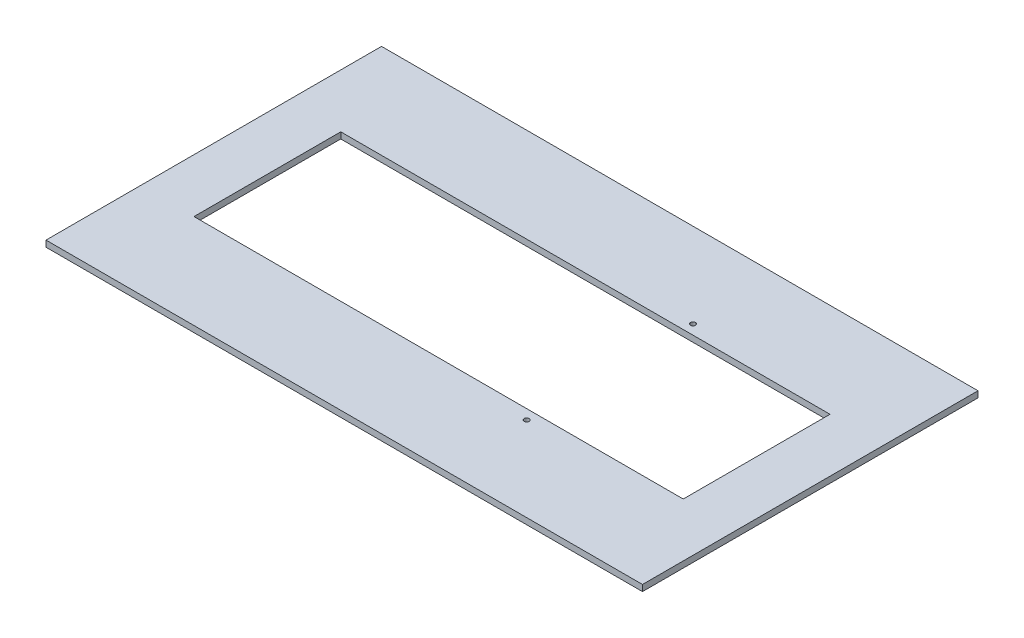
SolidWorks part; units mm, degrees
ref_plane "Front Plane" through (0, 0, 0) normal (0, 0, 1) x (1, 0, 0)
ref_plane "Top Plane" through (0, 0, 0) normal (0, 1, 0) x (1, 0, 0)
ref_plane "Right Plane" through (0, 0, 0) normal (1, 0, 0) x (0, 0, -1)
sketch "Sketch1" plane through (0, 0, 0) normal (0, 1, 0) x (1, 0, 0)
  line L1 (0, 0) -> (609.6, 0)
  line L2 (0, 0) -> (0, 342.9)
  line L3 (0, 342.9) -> (609.6, 342.9)
  line L4 (609.6, 0) -> (609.6, 342.9)
  line L5 (54.8, 246.45) -> (554.8, 246.45)
  line L6 (54.8, 246.45) -> (54.8, 96.45)
  line L7 (54.8, 96.45) -> (554.8, 96.45)
  line L8 (554.8, 246.45) -> (554.8, 96.45)
  circle A0 centre (404.8, 256.45) radius 2.555
  circle A1 centre (404.8, 86.45) radius 2.555
  point P4 (304.8, 246.45)
  point P10 (304.8, 342.9)
  point P11 (554.8, 171.45)
  point P12 (609.6, 171.45)
  dimension "D5" = 5.11
  dimension "D6" = 150
  dimension "D1" = 342.9
  dimension "D2" = 609.6
  dimension "D3" = 500
  dimension "D4" = 150
  dimension "D7" = 170
  dimension "D8" = 10
extrude "Boss-Extrude1" add sketch "Sketch1" along normal blind 6.35
sketch "Sketch2" plane through (0, 6.35, 0) normal (0, 1, 0) x (1, 0, 0)
  line L0 (511.8, 342.9) -> (511.8, 246.45)
  line L1 (554.8, 246.45) -> (54.8, 246.45) construction
  line L2 (609.6, 342.9) -> (0, 342.9) construction
  line L3 (554.8, 96.45) -> (554.8, 246.45) construction
  line L4 (511.8, 0) -> (511.8, 96.45)
  line L5 (54.8, 96.45) -> (554.8, 96.45) construction
  line L6 (0, 0) -> (609.6, 0) construction
  line L7 (411.8, 0) -> (411.8, 96.45)
  line L8 (411.8, 342.9) -> (411.8, 246.45)
  line L9 (311.8, 0) -> (311.8, 96.45)
  line L10 (311.8, 342.9) -> (311.8, 246.45)
  line L11 (211.8, 0) -> (211.8, 96.45)
  line L12 (211.8, 342.9) -> (211.8, 246.45)
  line L13 (111.8, 0) -> (111.8, 96.45)
  line L14 (111.8, 342.9) -> (111.8, 246.45)
  line L15 (461.8, 96.45) -> (461.8, 46.45)
  line L16 (361.8, 96.45) -> (361.8, 46.45)
  line L17 (261.8, 96.45) -> (261.8, 46.45)
  line L18 (161.8, 96.45) -> (161.8, 46.45)
  line L19 (361.8, 296.45) -> (361.8, 246.45)
  line L20 (261.8, 296.45) -> (261.8, 246.45)
  line L21 (161.8, 296.45) -> (161.8, 246.45)
  line L22 (461.8, 296.45) -> (461.8, 246.45)
  line L23 (501.8, 96.45) -> (501.8, 71.45)
  line L24 (491.8, 96.45) -> (491.8, 71.45)
  line L25 (481.8, 96.45) -> (481.8, 71.45)
  line L26 (471.8, 96.45) -> (471.8, 71.45)
  line L27 (461.8, 96.45) -> (461.8, 71.45)
  line L28 (451.8, 96.45) -> (451.8, 71.45)
  line L29 (441.8, 96.45) -> (441.8, 71.45)
  line L30 (431.8, 96.45) -> (431.8, 71.45)
  line L31 (421.8, 96.45) -> (421.8, 71.45)
  line L32 (411.8, 96.45) -> (411.8, 71.45)
  line L33 (401.8, 96.45) -> (401.8, 71.45)
  line L34 (391.8, 96.45) -> (391.8, 71.45)
  line L35 (381.8, 96.45) -> (381.8, 71.45)
  line L36 (371.8, 96.45) -> (371.8, 71.45)
  line L37 (361.8, 96.45) -> (361.8, 71.45)
  line L38 (351.8, 96.45) -> (351.8, 71.45)
  line L39 (341.8, 96.45) -> (341.8, 71.45)
  line L40 (331.8, 96.45) -> (331.8, 71.45)
  line L41 (321.8, 96.45) -> (321.8, 71.45)
  line L42 (311.8, 96.45) -> (311.8, 71.45)
  line L43 (301.8, 96.45) -> (301.8, 71.45)
  line L44 (291.8, 96.45) -> (291.8, 71.45)
  line L45 (281.8, 96.45) -> (281.8, 71.45)
  line L46 (271.8, 96.45) -> (271.8, 71.45)
  line L47 (261.8, 96.45) -> (261.8, 71.45)
  line L48 (251.8, 96.45) -> (251.8, 71.45)
  line L49 (241.8, 96.45) -> (241.8, 71.45)
  line L50 (231.8, 96.45) -> (231.8, 71.45)
  line L51 (221.8, 96.45) -> (221.8, 71.45)
  line L52 (211.8, 96.45) -> (211.8, 71.45)
  line L53 (201.8, 96.45) -> (201.8, 71.45)
  line L54 (191.8, 96.45) -> (191.8, 71.45)
  line L55 (181.8, 96.45) -> (181.8, 71.45)
  line L56 (171.8, 96.45) -> (171.8, 71.45)
  line L57 (161.8, 96.45) -> (161.8, 71.45)
  line L58 (151.8, 96.45) -> (151.8, 71.45)
  line L59 (141.8, 96.45) -> (141.8, 71.45)
  line L60 (131.8, 96.45) -> (131.8, 71.45)
  line L61 (121.8, 96.45) -> (121.8, 71.45)
  line L62 (491.8, 271.45) -> (491.8, 246.45)
  line L63 (481.8, 271.45) -> (481.8, 246.45)
  line L64 (471.8, 271.45) -> (471.8, 246.45)
  line L65 (461.8, 271.45) -> (461.8, 246.45)
  line L66 (451.8, 271.45) -> (451.8, 246.45)
  line L67 (441.8, 271.45) -> (441.8, 246.45)
  line L68 (431.8, 271.45) -> (431.8, 246.45)
  line L69 (421.8, 271.45) -> (421.8, 246.45)
  line L70 (411.8, 271.45) -> (411.8, 246.45)
  line L71 (401.8, 271.45) -> (401.8, 246.45)
  line L72 (391.8, 271.45) -> (391.8, 246.45)
  line L73 (381.8, 271.45) -> (381.8, 246.45)
  line L74 (371.8, 271.45) -> (371.8, 246.45)
  line L75 (361.8, 271.45) -> (361.8, 246.45)
  line L76 (351.8, 271.45) -> (351.8, 246.45)
  line L77 (341.8, 271.45) -> (341.8, 246.45)
  line L78 (331.8, 271.45) -> (331.8, 246.45)
  line L79 (321.8, 271.45) -> (321.8, 246.45)
  line L80 (311.8, 271.45) -> (311.8, 246.45)
  line L81 (301.8, 271.45) -> (301.8, 246.45)
  line L82 (291.8, 271.45) -> (291.8, 246.45)
  line L83 (281.8, 271.45) -> (281.8, 246.45)
  line L84 (271.8, 271.45) -> (271.8, 246.45)
  line L85 (261.8, 271.45) -> (261.8, 246.45)
  line L86 (251.8, 271.45) -> (251.8, 246.45)
  line L87 (241.8, 271.45) -> (241.8, 246.45)
  line L88 (231.8, 271.45) -> (231.8, 246.45)
  line L89 (221.8, 271.45) -> (221.8, 246.45)
  line L90 (211.8, 271.45) -> (211.8, 246.45)
  line L91 (201.8, 271.45) -> (201.8, 246.45)
  line L92 (191.8, 271.45) -> (191.8, 246.45)
  line L93 (181.8, 271.45) -> (181.8, 246.45)
  line L94 (171.8, 271.45) -> (171.8, 246.45)
  line L95 (161.8, 271.45) -> (161.8, 246.45)
  line L96 (151.8, 271.45) -> (151.8, 246.45)
  line L97 (141.8, 271.45) -> (141.8, 246.45)
  line L98 (131.8, 271.45) -> (131.8, 246.45)
  line L99 (121.8, 271.45) -> (121.8, 246.45)
  line L100 (501.8, 271.45) -> (501.8, 246.45)
  dimension "D1" = 43
  dimension "D3" = 50
  dimension "D4" = 50
  dimension "D7" = 25
  dimension "D8" = 10
  dimension "D2" = 5
  dimension "D5" = 4
  dimension "D6" = 2
  dimension "D9" = 2
